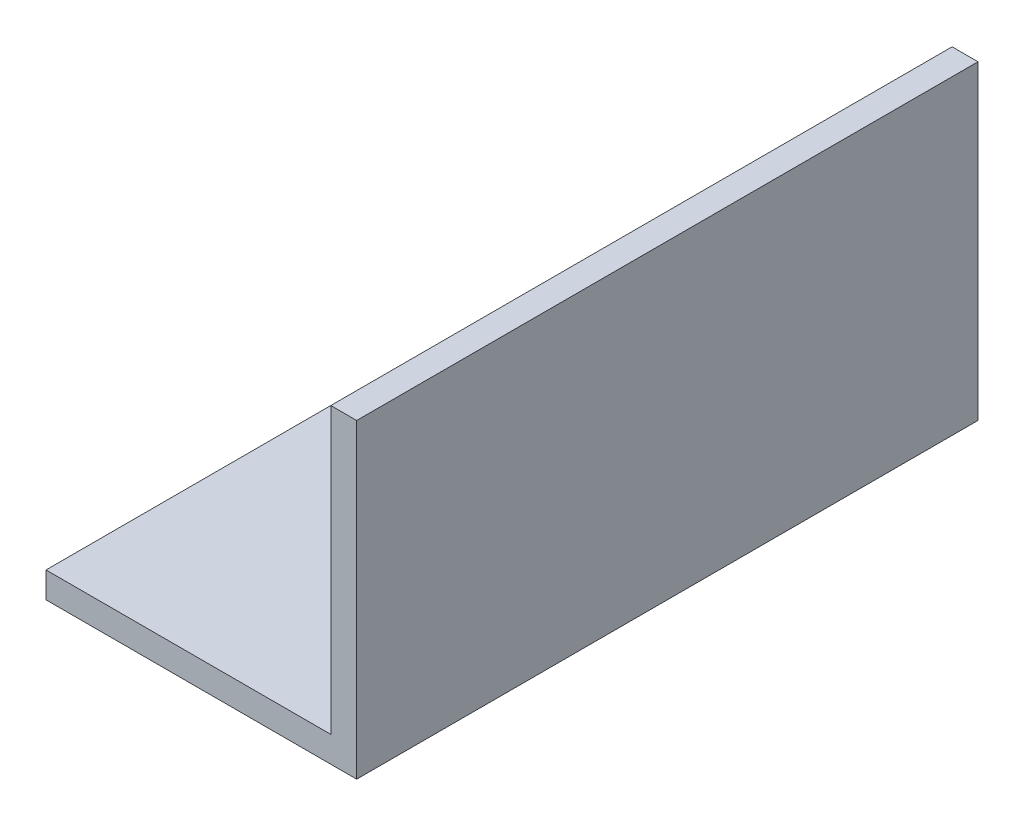
SolidWorks part; units mm, degrees
ref_plane "Front Plane" through (0, 0, 0) normal (0, 0, 1) x (1, 0, 0)
ref_plane "Top Plane" through (0, 0, 0) normal (0, 1, 0) x (1, 0, 0)
ref_plane "Right Plane" through (0, 0, 0) normal (1, 0, 0) x (0, 0, -1)
sketch "Sketch1" plane through (0, 0, 0) normal (0, 0, 1) x (0, -1, 0)
  line L0 (0, 0) -> (-38.1, 0)
  line L1 (-38.1, 0) -> (-38.1, -3.175)
  line L2 (-38.1, -3.175) -> (-3.175, -3.175)
  line L3 (-3.175, -3.175) -> (-3.175, -38.1)
  line L4 (-3.175, -38.1) -> (0, -38.1)
  line L5 (0, -38.1) -> (0, 0)
  dimension "D1" = 38.1
  dimension "D2" = 38.1
  dimension "D3" = 3.175
extrude "Boss-Extrude1" add sketch "Sketch1" along normal mid plane 76.2
sketch "Sketch2" plane through (0, 0, 0) normal (1, 0, 0) x (0, 0, -1)
  line L0 (-38.1, 19.05) -> (38.1, 19.05) construction
  line L1 (-38.1, 0) -> (-38.1, 38.1) construction
  line L2 (38.1, 0) -> (38.1, 38.1) construction
  line L3 (0, 38.1) -> (0, 0) construction
  line L4 (-38.1, 38.1) -> (38.1, 38.1) construction
sketch "Sketch3" plane through (0, 3.175, 0) normal (0, 1, 0) x (1, 0, 0)
  line L0 (-25.4, 0) -> (0, 0) construction
  line L1 (-38.1, -38.1) -> (-38.1, 38.1) construction
  circle A0 centre (-25.4, 0) radius 4.3656
  dimension "D1" = 8.7312
  dimension "D2" = 12.7
extrude "Cut-Extrude1" cut sketch "Sketch3" against normal up to next
